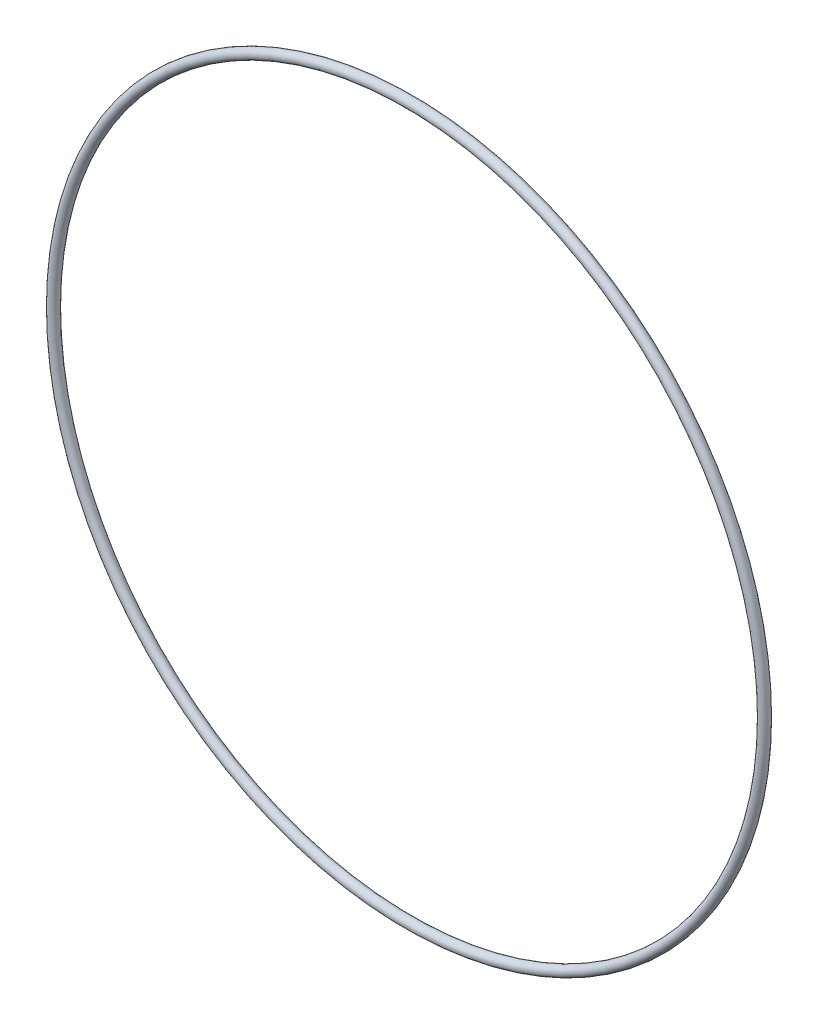
SolidWorks part; units mm, degrees
ref_plane "Front" through (0, 0, 0) normal (0, 0, 1) x (1, 0, 0)
ref_plane "Top" through (0, 0, 0) normal (0, 1, 0) x (1, 0, 0)
ref_plane "Right" through (0, 0, 0) normal (1, 0, 0) x (0, 0, -1)
sketch "Sketch1" plane through (0, 0, 0) normal (1, 0, 0) x (0, -1, 0)
  line L0 (0, -1.7653) -> (0, 1.7653) construction
  line L2 (-139.8676, 0) -> (139.8676, 0) construction
  line L3 (-123.6218, 0) -> (123.6218, 0) construction
  circle A0 centre (125.3871, 0) radius 1.7653
  point P9 (123.6218, 0)
  point P10 (127.1524, 0)
  point P13 (125.3871, 1.7653)
  point P14 (125.3871, -1.7653)
  dimension "Width" = 3.5306
  dimension "ID" = 247.2436
revolve "Revolve1" add sketch "Sketch1" angle 360 about L0
